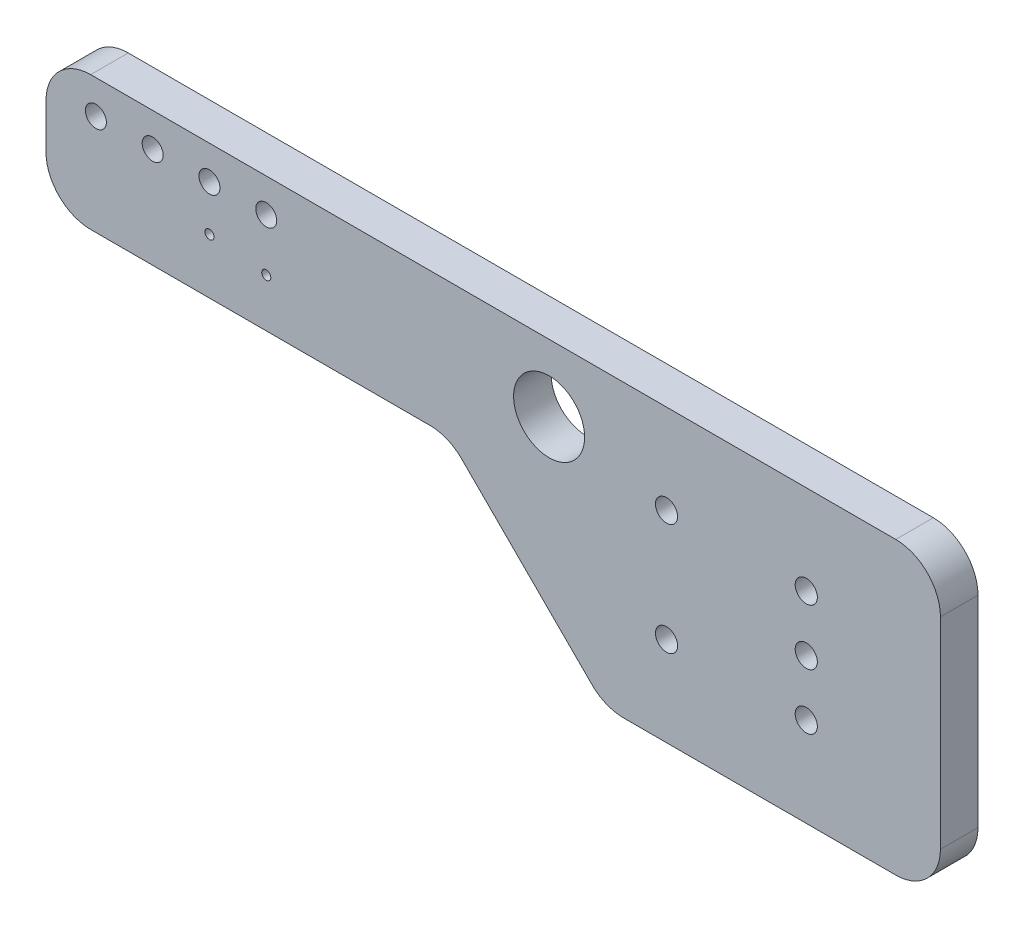
SolidWorks part; units mm, degrees
ref_plane "Front Plane" through (0, 0, 0) normal (0, 0, 1) x (1, 0, 0)
ref_plane "Top Plane" through (0, 0, 0) normal (0, 1, 0) x (1, 0, 0)
ref_plane "Right Plane" through (0, 0, 0) normal (1, 0, 0) x (0, 0, -1)
sketch "Sketch1" plane through (0, 0, 0) normal (0, 0, 1) x (1, 0, 0)
  line L0 (60, 63) -> (60, 61)
  line L1 (62, 59) -> (77.1716, 59)
  line L2 (78.5858, 58.4142) -> (84.4142, 52.5858)
  line L3 (85.8284, 52) -> (98, 52)
  line L4 (100, 54) -> (100, 63)
  line L5 (98, 65) -> (62, 65)
  arc A0 (62, 65) -> (60, 63) centre (62, 63) ccw
  arc A1 (60, 61) -> (62, 59) centre (62, 61) ccw
  arc A2 (77.1716, 59) -> (78.5858, 58.4142) centre (77.1716, 57) cw
  arc A3 (84.4142, 52.5858) -> (85.8284, 52) centre (85.8284, 54) ccw
  arc A4 (98, 52) -> (100, 54) centre (98, 54) ccw
  arc A5 (100, 63) -> (98, 65) centre (98, 63) ccw
extrude "BOARD" add sketch "Sketch1" along normal blind 1.68 separate body
sketch "Sketch2" plane through (0, 0, 0) normal (0, 0, 1) x (1, 0, 0)
  circle A0 centre (67.31, 61.468) radius 0.2032
  circle A1 centre (62.23, 63.5) radius 0.4699
  circle A2 centre (64.77, 63.5) radius 0.4699
  circle A3 centre (67.31, 63.5) radius 0.4699
  circle A4 centre (69.85, 61.1632) radius 0.2032
  circle A5 centre (69.85, 63.5) radius 0.4699
  circle A6 centre (82.5, 62) radius 1.5875
  circle A7 centre (87.75, 56) radius 0.4953
  circle A8 centre (87.75, 61) radius 0.4953
  circle A9 centre (94, 58.5) radius 0.4953
  circle A10 centre (94, 56) radius 0.4953
  circle A11 centre (94, 61) radius 0.4953
extrude "PLATED HOLES" cut sketch "Sketch2" along normal through all
ref_plane "Plane1" through (0, 0, 0.8992) normal (0, 0, 1) x (1, 0, 0)
sketch "Sketch3" plane through (0, 0, 0) normal (0, 0, 1) x (1, 0, 0)
  line L0 (85.6, 63.45) -> (100.1, 63.45)
  line L1 (100.1, 63.45) -> (100.1, 53.55)
  line L2 (100.1, 53.55) -> (85.6, 53.55)
  line L3 (85.6, 53.55) -> (85.6, 63.45)
extrude "ENCODER_PEC09-2320F-S0015-1" [suppressed] add sketch "Sketch3" against normal blind 0.0254
